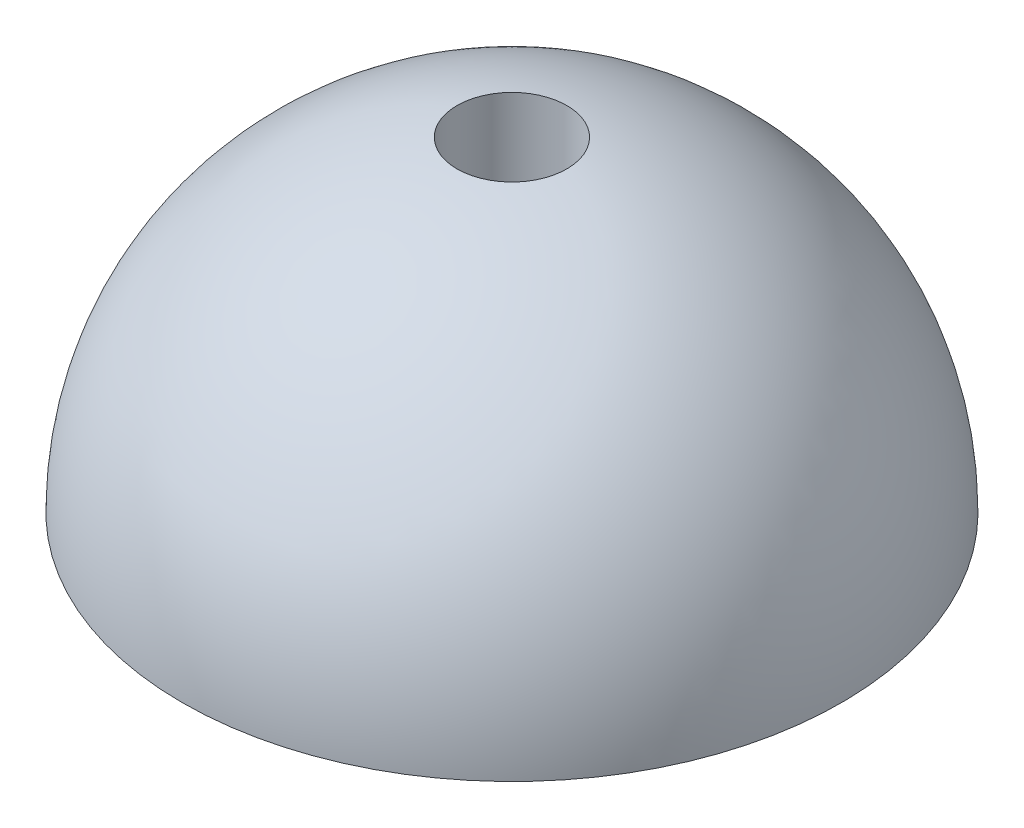
SolidWorks part; units mm, degrees
ref_plane "前视基准面" through (0, 0, 0) normal (0, 0, 1) x (1, 0, 0)
ref_plane "上视基准面" through (0, 0, 0) normal (0, 1, 0) x (1, 0, 0)
ref_plane "右视基准面" through (0, 0, 0) normal (1, 0, 0) x (0, 0, -1)
sketch "草图2" plane through (0, 0, 0) normal (0, 0, 1) x (1, 0, 0)
  line L0 (5, 0) -> (30, 0)
  line L2 (0, 0) -> (0, -31.6981) construction
  line L3 (5, 0) -> (5, 29.5804)
  arc A0 (30, 0) -> (5, 29.5804) centre (0, 0) ccw
revolve "旋转1" add sketch "草图2" angle 360 about L2
